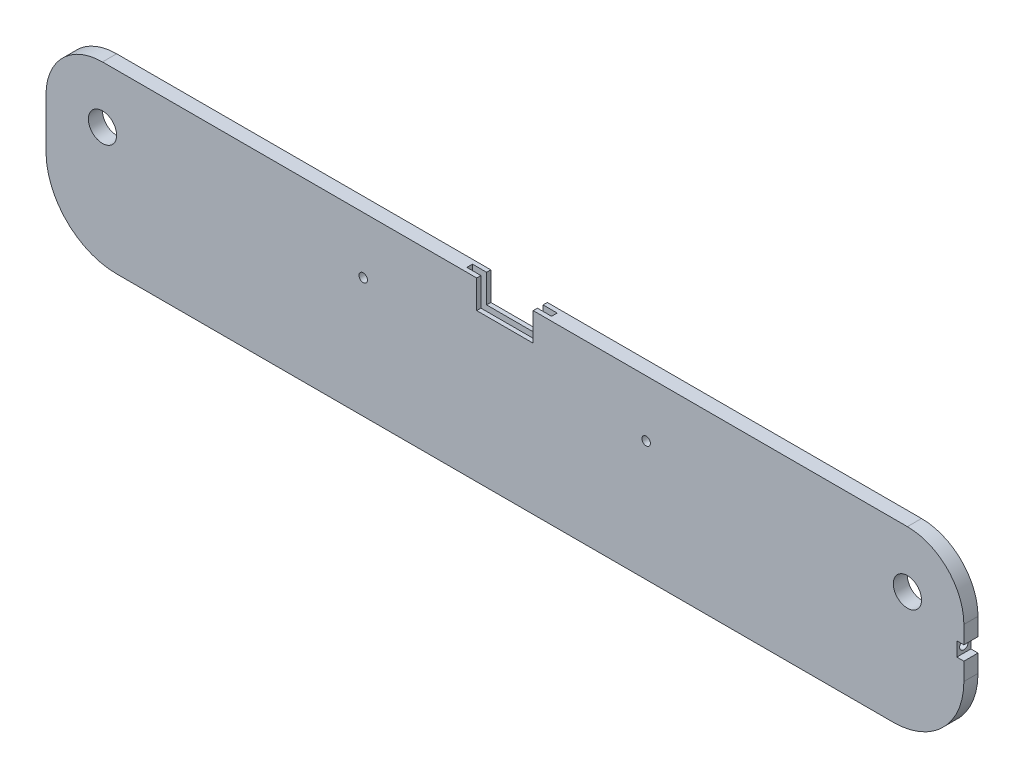
SolidWorks part; units mm, degrees
ref_plane "Front Plane" through (0, 0, 0) normal (0, 0, 1) x (1, 0, 0)
ref_plane "Top Plane" through (0, 0, 0) normal (0, 1, 0) x (1, 0, 0)
ref_plane "Right Plane" through (0, 0, 0) normal (1, 0, 0) x (0, 0, -1)
sketch "Sketch1" plane through (0, 0, 0) normal (0, 0, 1) x (1, 0, 0)
  line L1 (-47.1041, 88.3097) -> (602.8959, 88.3097)
  line L2 (-47.1041, 88.3097) -> (-47.1041, -36.6903)
  line L3 (-47.1041, -36.6903) -> (602.8959, -36.6903)
  line L4 (602.8959, 88.3097) -> (602.8959, -36.6903)
extrude "Boss-Extrude1" add sketch "Sketch1" along normal blind 10
sketch "Sketch2" plane through (0, 0, 10) normal (0, 0, 1) x (1, 0, 0)
  circle A0 centre (-7.1041, 48.3097) radius 10
extrude "Cut-Extrude2" cut sketch "Sketch2" against normal blind 10 contours A0
sketch "Sketch3" plane through (0, 0, 10) normal (0, 0, 1) x (1, 0, 0)
  circle A1 centre (562.8959, 48.3097) radius 10
extrude "Cut-Extrude3" cut sketch "Sketch3" against normal blind 10
sketch "Sketch7" plane through (0, 0, 10) normal (0, 0, 1) x (1, 0, 0)
  line L24 (160.8959, 25.3097) -> (158.8959, 25.3097)
  line L25 (98.8959, 25.3097) -> (96.8959, 25.3097)
  line L26 (89.8959, 25.3097) -> (91.8959, 25.3097)
  line L27 (29.8959, 25.3097) -> (27.8959, 25.3097)
  line L28 (158.8959, -34.6903) -> (158.8959, 25.3097)
  line L29 (98.8959, -34.6903) -> (158.8959, -34.6903)
  line L30 (98.8959, 25.3097) -> (98.8959, -34.6903)
  line L31 (89.8959, -34.6903) -> (89.8959, 25.3097)
  line L32 (29.8959, -34.6903) -> (89.8959, -34.6903)
  line L33 (29.8959, -34.6903) -> (29.8959, 25.3097)
  line L34 (160.8959, -36.6903) -> (160.8959, 25.3097)
  line L35 (96.8959, -36.6903) -> (160.8959, -36.6903)
  line L36 (96.8959, 25.3097) -> (96.8959, -36.6903)
  line L37 (27.8959, -36.6903) -> (27.8959, 25.3097)
  line L38 (91.8959, -36.6903) -> (91.8959, 25.3097)
  line L39 (27.8959, -36.6903) -> (91.8959, -36.6903)
sketch "Sketch8" plane through (0, 0, 10) normal (0, 0, 1) x (1, 0, 0)
  circle A0 centre (177.5091, 48.3097) radius 3
  circle A1 centre (377.8959, 48.3097) radius 3
extrude "Cut-Extrude5" cut sketch "Sketch8" against normal blind 20
sketch "Sketch9" plane through (0, 0, 10) normal (0, 0, 1) x (1, 0, 0)
  line L1 (277.8959, 68.3097) -> (257.8959, 68.3097)
  line L2 (257.8959, 68.3097) -> (257.8959, 88.3097)
  line L3 (602.8959, 88.3097) -> (-47.1041, 88.3097) construction
  line L4 (257.8959, 88.3097) -> (297.8959, 88.3097)
  line L5 (297.8959, 88.3097) -> (297.8959, 68.3097)
  line L6 (297.8959, 68.3097) -> (277.8959, 68.3097)
sketch "Sketch10" plane through (0, 88.3097, 0) normal (0, 1, 0) x (1, 0, 0)
  line L0 (602.8959, -10) -> (-47.1041, -10) construction
  line L4 (277.8959, -3) -> (307.8959, -3)
  line L5 (307.8959, -3) -> (307.8959, -7)
  line L6 (307.8959, -7) -> (277.8959, -7)
  line L7 (277.8959, -7) -> (247.8959, -7)
  line L8 (247.8959, -7) -> (247.8959, -3)
  line L9 (247.8959, -3) -> (277.8959, -3)
  dimension "D2" = 3
extrude "Cut-Extrude7" cut sketch "Sketch10" against normal blind 30
extrude "Cut-Extrude8" cut sketch "Sketch9" against normal blind 30
extrude "Boss-Extrude5" add sketch "Sketch7" along normal blind 20
sketch "Sketch12" plane through (602.8959, 0, 0) normal (1, 0, 0) x (0, 0, -1)
  line L0 (-10, -36.6903) -> (-10, 88.3097) construction
  line L1 (-10, 25.8097) -> (0, 25.8097)
  line L2 (-10, 25.8097) -> (-10, 35.8097)
  line L3 (-10, 35.8097) -> (0, 35.8097)
  line L4 (0, 25.8097) -> (0, 35.8097)
  line L5 (0, -36.6903) -> (0, 88.3097) construction
extrude "Cut-Extrude9" cut sketch "Sketch12" against normal blind 5
sketch "Sketch13" plane through (597.8959, 0, 0) normal (1, 0, 0) x (0, 0, -1)
  circle A0 centre (-5, 30.8097) radius 3
extrude "Cut-Extrude10" cut sketch "Sketch13" against normal blind 5
fillet "Fillet3" radius 50 1 edges at (602.8959, -36.6903, 5)
fillet "Fillet5" radius 40 1 edges at (602.8959, 88.3097, 5)
fillet "Fillet6" radius 50 1 edges at (-47.1041, -36.6903, 5)
fillet "Fillet7" radius 40 1 edges at (-47.1041, 88.3097, 5)
sketch "Sketch14" plane through (0, -36.6903, 0) normal (0, -1, 0) x (1, 0, 0)
  line L1 (27.8959, 30) -> (160.8959, 30)
  line L2 (27.8959, 30) -> (27.8959, 10)
  line L3 (27.8959, 10) -> (160.8959, 10)
  line L4 (160.8959, 30) -> (160.8959, 10)
extrude "Cut-Extrude11" cut sketch "Sketch14" against normal blind 80
